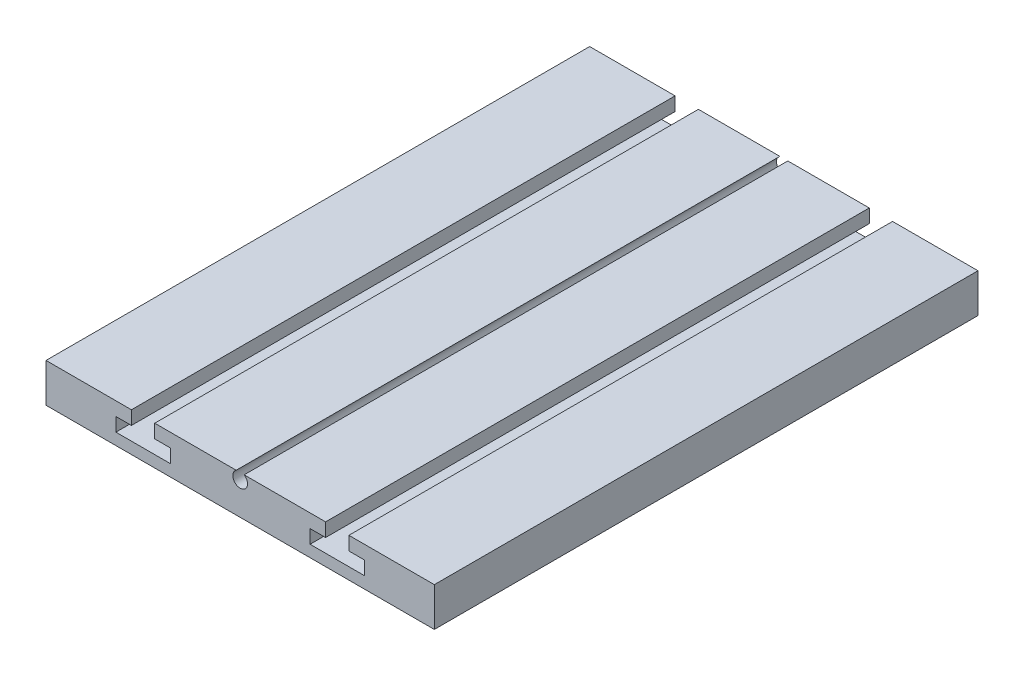
SolidWorks part; units mm, degrees
ref_plane "Front Plane" through (0, 0, 0) normal (0, 0, 1) x (1, 0, 0)
ref_plane "Top Plane" through (0, 0, 0) normal (0, 1, 0) x (1, 0, 0)
ref_plane "Right Plane" through (0, 0, 0) normal (1, 0, 0) x (0, 0, -1)
sketch "Sketch1" plane through (0, 0, 0) normal (0, 0, 1) x (1, 0, 0)
  line L1 (0, 0) -> (50, 0)
  line L2 (0, 0) -> (0, 5)
  line L3 (0, 5) -> (50, 5)
  line L4 (50, 0) -> (50, 5)
  dimension "D1" = 50
  dimension "D2" = 5
extrude "Boss-Extrude1" add sketch "Sketch1" along normal blind 70
sketch "Sketch3" plane through (0, 0, 70) normal (0, 0, 1) x (1, 0, 0)
  line L0 (25, 5) -> (25, 0) construction
  line L1 (50, 5) -> (0, 5) construction
  line L2 (0, 0) -> (50, 0) construction
  line L3 (0, 2.5) -> (50, 2.5) construction
  line L4 (0, 5) -> (0, 0) construction
  line L5 (50, 0) -> (50, 5) construction
  line L6 (14, 3.25) -> (16, 3.25)
  line L7 (9, 3.25) -> (11, 3.25)
  line L8 (9, 3.25) -> (9, 1.5)
  line L9 (9, 1.5) -> (16, 1.5)
  line L10 (16, 3.25) -> (16, 1.5)
  line L19 (11, 5) -> (14, 5)
  line L20 (11, 5) -> (11, 3.25)
  line L22 (14, 5) -> (14, 3.25)
  line L23 (12.5, 5) -> (12.5, 3.25) construction
  line L24 (12.5, 3.25) -> (0, 3.25) construction
  line L25 (41, 3.25) -> (41, 1.5)
  line L26 (41, 1.5) -> (34, 1.5)
  line L27 (34, 3.25) -> (34, 1.5)
  line L28 (36, 3.25) -> (34, 3.25)
  line L29 (36, 5) -> (36, 3.25)
  line L30 (39, 5) -> (36, 5)
  line L31 (39, 5) -> (39, 3.25)
  line L32 (41, 3.25) -> (39, 3.25)
  circle A1 centre (25, 4.2) radius 0.95
  dimension "D1" = 1.9
  dimension "D2" = 0.8
  dimension "D3" = 3
  dimension "D4" = 2
  dimension "D5" = 12.5
  dimension "D6" = 1.75
extrude "Cut-Extrude2" cut sketch "Sketch3" against normal through all
